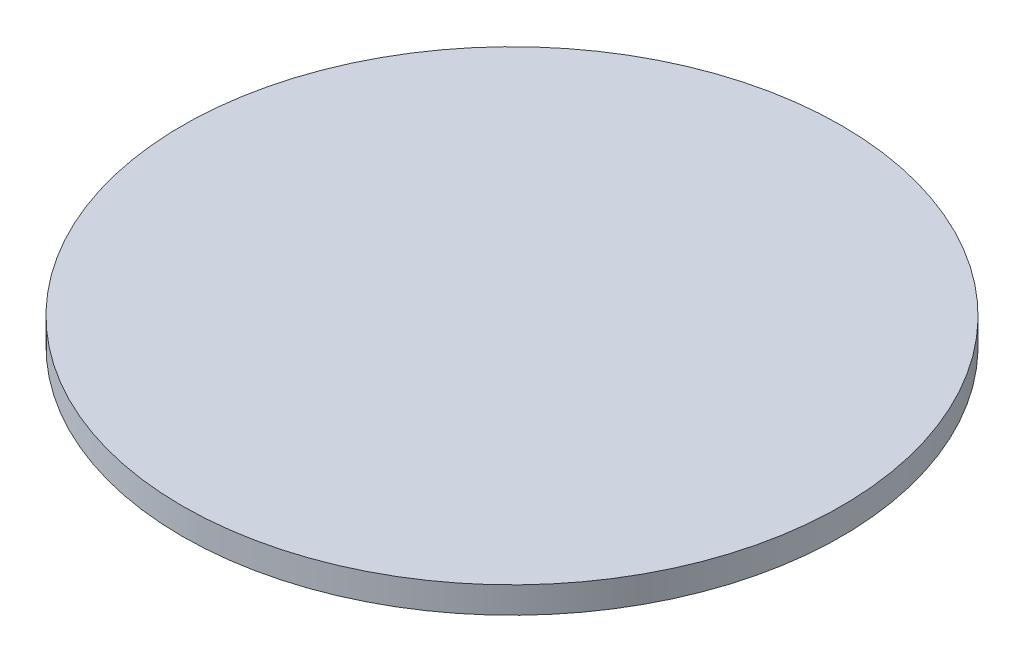
SolidWorks part; units mm, degrees
ref_plane "前基準面" through (0, 0, 0) normal (0, 0, 1) x (1, 0, 0)
ref_plane "上基準面" through (0, 0, 0) normal (0, 1, 0) x (1, 0, 0)
ref_plane "右基準面" through (0, 0, 0) normal (1, 0, 0) x (0, 0, -1)
sketch "草圖1" plane through (0, 0, 0) normal (0, 1, 0) x (1, 0, 0)
  circle A0 centre (-1.5712, 0) radius 25
  dimension "D1" = 50
extrude "填料-伸長1" add sketch "草圖1" along normal blind 2
